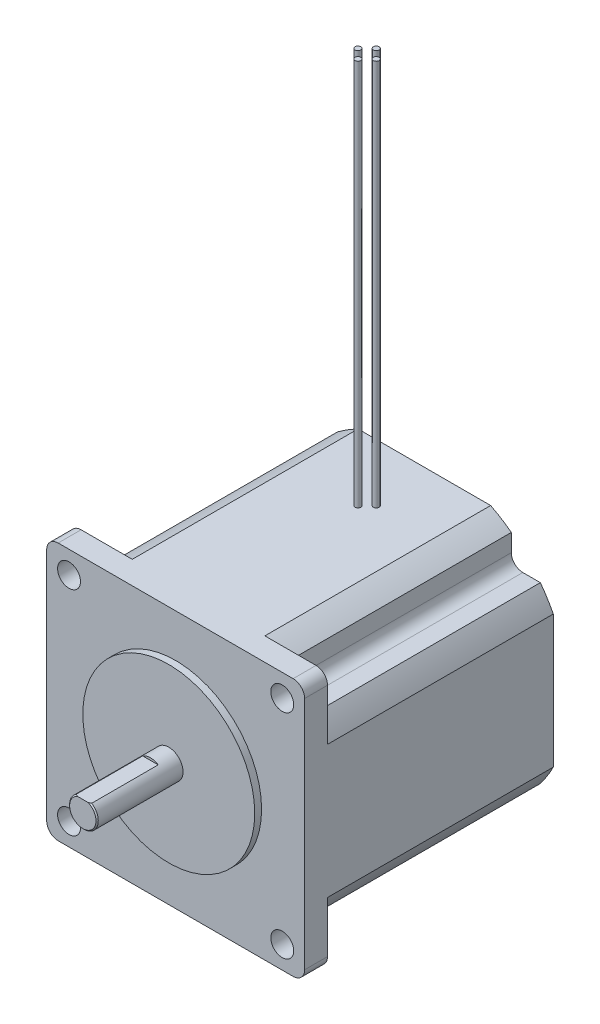
SolidWorks part; units mm, degrees
material "Plain Carbon Steel"
ref_plane "Front Plane" through (0, 0, 0) normal (0, 0, 1) x (1, 0, 0)
ref_plane "Top Plane" through (0, 0, 0) normal (0, 1, 0) x (1, 0, 0)
ref_plane "Right Plane" through (0, 0, 0) normal (1, 0, 0) x (0, 0, -1)
ref_plane "Plane1" through (0, 0, 55.118) normal (0, 0, 1) x (1, 0, 0)
sketch "Sketch1" plane through (0, 0, 55.118) normal (0, 0, 1) x (1, 0, 0)
  line L0 (28.575, -28.575) -> (28.575, 28.575)
  line L1 (28.575, 28.575) -> (-28.575, 28.575)
  line L2 (-28.575, 28.575) -> (-28.575, -28.575)
  line L3 (-28.575, -28.575) -> (28.575, -28.575)
extrude "Boss-Extrude1" add sketch "Sketch1" against normal blind 55.118
sketch "Sketch2" plane through (0, 0, 0) normal (0, 0, -1) x (-1, 0, 0)
  line L0 (-28.575, -28.575) -> (-14.6925, -28.575)
  line L1 (-28.575, -14.6925) -> (-28.575, -28.575)
  arc A0 (-14.6925, -28.575) -> (-28.575, -14.6925) centre (0, 0) cw
extrude "Cut-Extrude1" cut sketch "Sketch2" against normal blind 50.038
sketch "Sketch3" plane through (0, 0, 0) normal (0, 0, -1) x (-1, 0, 0)
  line L0 (-19.2786, -25.7048) -> (-19.2786, -19.2786)
  line L1 (-19.2786, -19.2786) -> (-25.7048, -19.2786)
  arc A0 (-25.7048, -19.2786) -> (-19.2786, -25.7048) centre (0, 0) ccw
extrude "Cut-Extrude2" cut sketch "Sketch3" against normal blind 50.038
sketch "Sketch4" plane through (0, 0, 0) normal (0, 0, -1) x (-1, 0, 0)
  line L0 (-28.575, 28.575) -> (-28.575, 14.6925)
  line L1 (-14.6925, 28.575) -> (-28.575, 28.575)
  arc A0 (-28.575, 14.6925) -> (-14.6925, 28.575) centre (0, 0) cw
extrude "Cut-Extrude3" cut sketch "Sketch4" against normal blind 50.038
sketch "Sketch5" plane through (0, 0, 0) normal (0, 0, -1) x (-1, 0, 0)
  line L0 (-25.7048, 19.2786) -> (-19.2786, 19.2786)
  line L1 (-19.2786, 19.2786) -> (-19.2786, 25.7048)
  arc A0 (-19.2786, 25.7048) -> (-25.7048, 19.2786) centre (0, 0) ccw
extrude "Cut-Extrude4" cut sketch "Sketch5" against normal blind 50.038
sketch "Sketch6" plane through (0, 0, 0) normal (0, 0, -1) x (-1, 0, 0)
  line L0 (28.575, 28.575) -> (14.6925, 28.575)
  line L1 (28.575, 14.6925) -> (28.575, 28.575)
  arc A0 (14.6925, 28.575) -> (28.575, 14.6925) centre (0, 0) cw
extrude "Cut-Extrude5" cut sketch "Sketch6" against normal blind 50.038
sketch "Sketch7" plane through (0, 0, 0) normal (0, 0, -1) x (-1, 0, 0)
  line L0 (19.2786, 25.7048) -> (19.2786, 19.2786)
  line L1 (19.2786, 19.2786) -> (25.7048, 19.2786)
  arc A0 (25.7048, 19.2786) -> (19.2786, 25.7048) centre (0, 0) ccw
extrude "Cut-Extrude6" cut sketch "Sketch7" against normal blind 50.038
sketch "Sketch8" plane through (0, 0, 0) normal (0, 0, -1) x (-1, 0, 0)
  line L0 (28.575, -28.575) -> (28.575, -14.6925)
  line L1 (14.6925, -28.575) -> (28.575, -28.575)
  arc A0 (28.575, -14.6925) -> (14.6925, -28.575) centre (0, 0) cw
extrude "Cut-Extrude7" cut sketch "Sketch8" against normal blind 50.038
sketch "Sketch9" plane through (0, 0, 0) normal (0, 0, -1) x (-1, 0, 0)
  line L0 (25.7048, -19.2786) -> (19.2786, -19.2786)
  line L1 (19.2786, -19.2786) -> (19.2786, -25.7048)
  arc A0 (19.2786, -25.7048) -> (25.7048, -19.2786) centre (0, 0) ccw
extrude "Cut-Extrude8" cut sketch "Sketch9" against normal blind 50.038
sketch "Sketch10" plane through (0, 0, 55.118) normal (0, 0, 1) x (1, 0, 0)
  circle A0 centre (0, 0) radius 19.05
extrude "Boss-Extrude2" add sketch "Sketch10" along normal blind 1.524
sketch "Sketch11" plane through (0, 0, 56.642) normal (0, 0, 1) x (1, 0, 0)
  circle A0 centre (0, 0) radius 3.175
extrude "Boss-Extrude3" add sketch "Sketch11" along normal blind 19.05
sketch "Sketch12" plane through (0, 0, 75.692) normal (0, 0, 1) x (1, 0, 0)
  line L0 (-1.7227, 2.667) -> (1.7227, 2.667)
  arc A0 (1.7227, 2.667) -> (-1.7227, 2.667) centre (0, 0) ccw
extrude "Cut-Extrude9" cut sketch "Sketch12" against normal blind 14.986
ref_plane "Plane2" through (0, 0, 12.7) normal (0, 0, -1) x (-1, 0, 0)
sketch "Sketch13" plane through (0, 0, 12.7) normal (0, 0, -1) x (-1, 0, 0)
  line L0 (1.397, 28.575) -> (2.032, 28.575)
  line L1 (2.032, 28.575) -> (2.032, 114.3)
  line L2 (2.032, 114.3) -> (1.397, 114.3)
  line L3 (1.397, 114.3) -> (1.397, 28.575)
  line L4 (2.032, 28.575) -> (2.032, 114.3) construction
revolve "Revolve1" add sketch "Sketch13" angle 360 about L4
sketch "Sketch14" plane through (0, 0, 12.7) normal (0, 0, -1) x (-1, 0, 0)
  line L0 (-2.667, 28.575) -> (-2.032, 28.575)
  line L1 (-2.032, 28.575) -> (-2.032, 114.3)
  line L2 (-2.032, 114.3) -> (-2.667, 114.3)
  line L3 (-2.667, 114.3) -> (-2.667, 28.575)
  line L4 (-2.032, 28.575) -> (-2.032, 114.3) construction
revolve "Revolve2" add sketch "Sketch14" angle 360 about L4
ref_plane "Plane3" through (0, 0, 14.732) normal (0, 0, -1) x (-1, 0, 0)
sketch "Sketch15" plane through (0, 0, 14.732) normal (0, 0, -1) x (-1, 0, 0)
  line L0 (-0.635, 28.575) -> (0, 28.575)
  line L1 (0, 28.575) -> (0, 114.3)
  line L2 (0, 114.3) -> (-0.635, 114.3)
  line L3 (-0.635, 114.3) -> (-0.635, 28.575)
  line L4 (0, 28.575) -> (0, 114.3) construction
revolve "Revolve3" add sketch "Sketch15" angle 360 about L4
ref_plane "Plane4" through (0, 0, 10.668) normal (0, 0, -1) x (-1, 0, 0)
sketch "Sketch16" plane through (0, 0, 10.668) normal (0, 0, -1) x (-1, 0, 0)
  line L0 (-0.635, 28.575) -> (0, 28.575)
  line L1 (0, 28.575) -> (0, 114.3)
  line L2 (0, 114.3) -> (-0.635, 114.3)
  line L3 (-0.635, 114.3) -> (-0.635, 28.575)
  line L4 (0, 28.575) -> (0, 114.3) construction
revolve "Revolve4" add sketch "Sketch16" angle 360 about L4
hole_wizard "Hole1" positions "Sketch18" profile "Sketch17" legacy
sketch "Sketch18" plane through (0, 0, 50.038) normal (0, 0, -1) x (-1, 0, 0)
  point P0 (23.622, -23.622)
sketch "Sketch17" plane through (-23.622, -23.622, 50.038) normal (1, 0, 0) x (0, 1, 0)
  line L0 (0, 0) -> (0, 25.654)
  line L1 (0, 25.654) -> (2.54, 25.654)
  line L2 (2.54, 25.654) -> (2.54, 0)
  line L3 (2.54, 0) -> (0, 0)
  line L4 (0, 110) -> (0, -10) construction
  dimension "Diameter" = 5.08
  dimension "Depth" = 25.654
hole_wizard "Hole2" positions "Sketch20" profile "Sketch19" legacy
sketch "Sketch20" plane through (0, 0, 50.038) normal (0, 0, -1) x (-1, 0, 0)
  point P0 (23.622, 23.622)
sketch "Sketch19" plane through (-23.622, 23.622, 50.038) normal (1, 0, 0) x (0, 1, 0)
  line L0 (0, 0) -> (0, 25.654)
  line L1 (0, 25.654) -> (2.54, 25.654)
  line L2 (2.54, 25.654) -> (2.54, 0)
  line L3 (2.54, 0) -> (0, 0)
  line L4 (0, 110) -> (0, -10) construction
  dimension "Diameter" = 5.08
  dimension "Depth" = 25.654
hole_wizard "Hole3" positions "Sketch22" profile "Sketch21" legacy
sketch "Sketch22" plane through (0, 0, 50.038) normal (0, 0, -1) x (-1, 0, 0)
  point P0 (-23.622, 23.622)
sketch "Sketch21" plane through (23.622, 23.622, 50.038) normal (1, 0, 0) x (0, 1, 0)
  line L0 (0, 0) -> (0, 25.654)
  line L1 (0, 25.654) -> (2.54, 25.654)
  line L2 (2.54, 25.654) -> (2.54, 0)
  line L3 (2.54, 0) -> (0, 0)
  line L4 (0, 110) -> (0, -10) construction
  dimension "Diameter" = 5.08
  dimension "Depth" = 25.654
hole_wizard "Hole4" positions "Sketch24" profile "Sketch23" legacy
sketch "Sketch24" plane through (0, 0, 50.038) normal (0, 0, -1) x (-1, 0, 0)
  point P0 (-23.622, -23.622)
sketch "Sketch23" plane through (23.622, -23.622, 50.038) normal (1, 0, 0) x (0, 1, 0)
  line L0 (0, 0) -> (0, 25.654)
  line L1 (0, 25.654) -> (2.54, 25.654)
  line L2 (2.54, 25.654) -> (2.54, 0)
  line L3 (2.54, 0) -> (0, 0)
  line L4 (0, 110) -> (0, -10) construction
  dimension "Diameter" = 5.08
  dimension "Depth" = 25.654
chamfer "Chamfer1" distance 0.254 angle 45 1 edges at (0, -3.175, 75.692)
fillet "Fillet1" radius 2.54 1 edges at (-28.575, 28.575, 52.578)
fillet "Fillet2" radius 2.54 1 edges at (-28.575, -28.575, 52.578)
fillet "Fillet3" radius 2.54 1 edges at (28.575, 28.575, 52.578)
fillet "Fillet4" radius 2.54 1 edges at (-19.2786, 19.2786, 25.019)
fillet "Fillet5" radius 2.54 1 edges at (28.575, -28.575, 52.578)
fillet "Fillet6" radius 2.54 1 edges at (19.2786, -19.2786, 25.019)
fillet "Fillet7" radius 2.54 1 edges at (19.2786, 19.2786, 25.019)
fillet "Fillet8" radius 2.54 1 edges at (-19.2786, -19.2786, 25.019)
